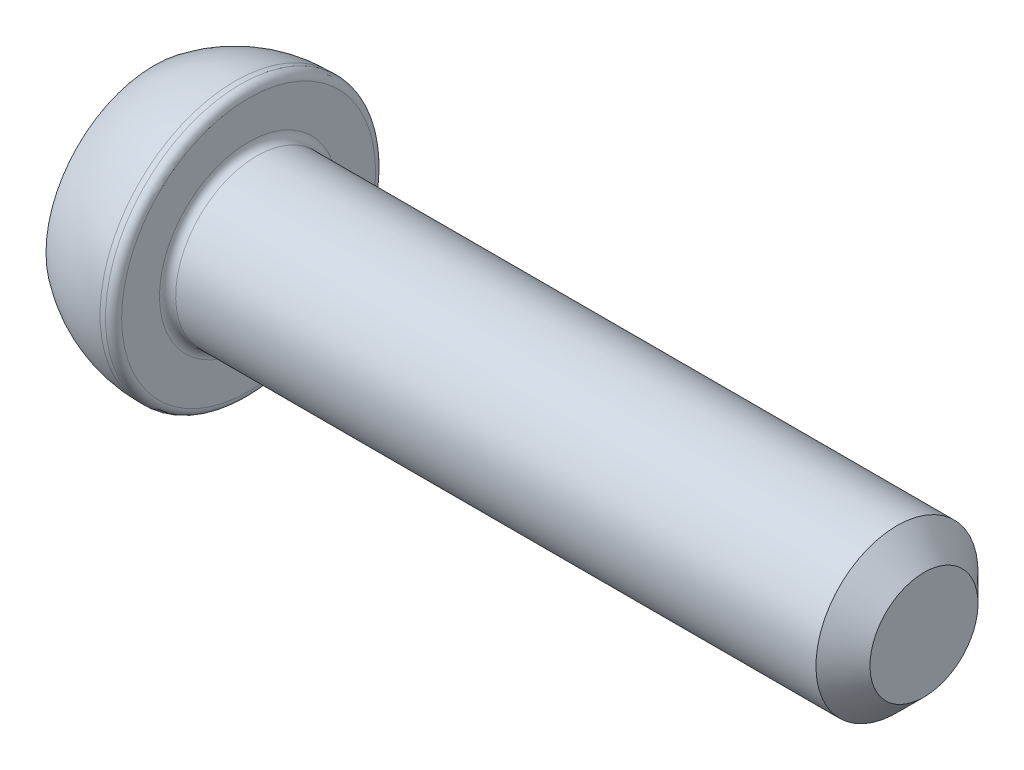
SolidWorks part; units mm, degrees
ref_plane "Спереди" through (0, 0, 0) normal (0, 0, 1) x (1, 0, 0)
ref_plane "Сверху" through (0, 0, 0) normal (0, 1, 0) x (1, 0, 0)
ref_plane "Справа" through (0, 0, 0) normal (1, 0, 0) x (0, 0, -1)
sketch "Эскиз1" plane through (0, 0, 0) normal (0, 0, 1) x (1, 0, 0)
  line L0 (0, 0) -> (0, 4)
  line L1 (3, 5) -> (3.5, 5)
  line L2 (3.5, 5) -> (3.5, 3)
  line L3 (3.5, 3) -> (28.5, 3)
  line L4 (28.5, 3) -> (28.5, 0)
  line L5 (28.5, 0) -> (0, 0) construction
  line L6 (0, 0) -> (28.5, 0)
  arc A0 (0, 4) -> (3, 5) centre (3, 0) cw
  point P9 (3.5, 4)
  dimension "D1" = 0.5
  dimension "D2" = 6
  dimension "D3" = 10
  dimension "D5" = 3.5
  dimension "D6" = 25
revolve "Повернуть1" add sketch "Эскиз1" angle 360 about L5
cosmetic thread "Условное изображение резьбы1" parameters "D2"=4.891
sketch "Эскиз2" plane through (0, 0, 0) normal (-1, 0, 0) x (0, 0, 1)
  line L1 (1.1547, 2) -> (-1.1547, 2)
  line L2 (-1.1547, 2) -> (-2.3094, 0)
  line L3 (-2.3094, 0) -> (-1.1547, -2)
  line L4 (-1.1547, -2) -> (1.1547, -2)
  line L5 (1.1547, -2) -> (2.3094, 0)
  line L6 (2.3094, 0) -> (1.1547, 2)
  circle A0 centre (0, 0) radius 2 construction
  dimension "D1" = 4
extrude "Вырез-Вытянуть1" cut sketch "Эскиз2" against normal blind 2
fillet "Скругление1" radius 0.3 2 edges at (3.5, 3, 0) (3.5, 5, 0)
chamfer "Фаска1" distance 1 angle 45 1 edges at (28.5, 3, 0)
